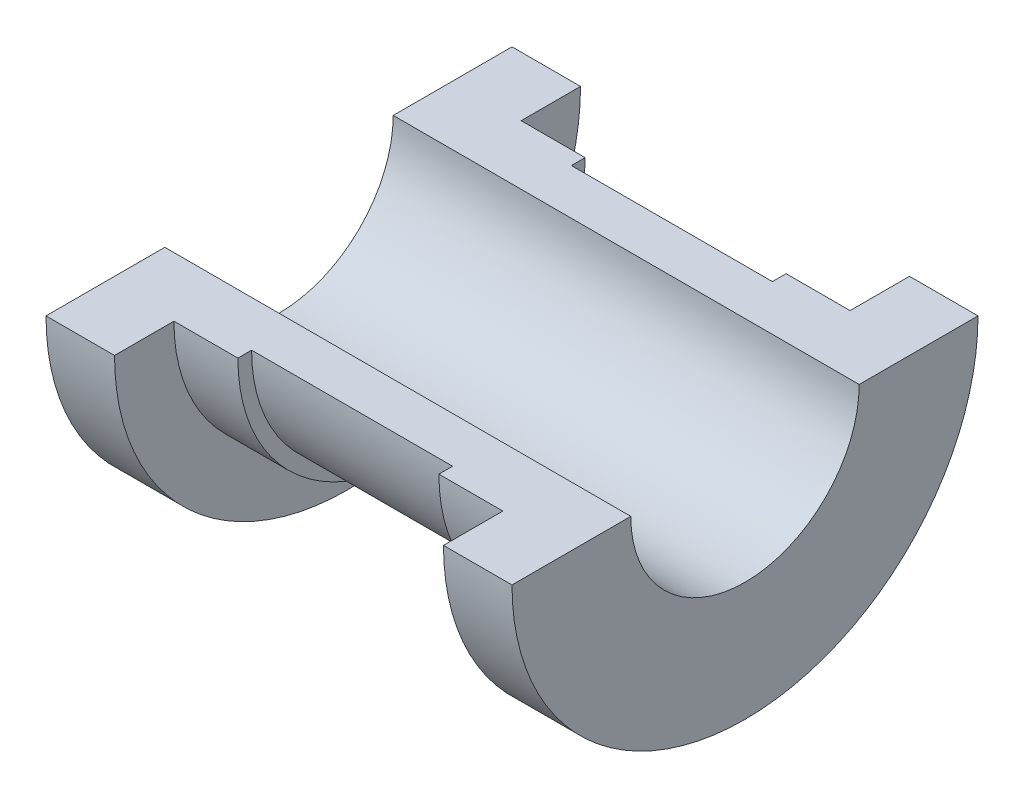
SolidWorks part; units mm, degrees
ref_plane "Front Plane" through (0, 0, 0) normal (0, 0, 1) x (1, 0, 0)
ref_plane "Top Plane" through (0, 0, 0) normal (0, 1, 0) x (1, 0, 0)
ref_plane "Right Plane" through (0, 0, 0) normal (1, 0, 0) x (0, 0, -1)
sketch "Sketch2" plane through (0, 0, 0) normal (0, 1, 0) x (1, 0, 0)
  line L0 (0, 0) -> (0, 66.6493) construction
  line L1 (25.5, 0) -> (-25.5, 0)
  line L2 (-25.5, 0) -> (-25.5, 25.5)
  line L3 (-18, 25.5) -> (-18, 19)
  line L4 (-18, 19) -> (-11, 19)
  line L5 (-11, 19) -> (-11, 17.5)
  line L6 (-11, 17.5) -> (11, 17.5)
  line L7 (-25.5, 25.5) -> (-18, 25.5)
  line L8 (25.5, 25.5) -> (18, 25.5)
  line L9 (11, 19) -> (11, 17.5)
  line L10 (18, 19) -> (11, 19)
  line L11 (18, 25.5) -> (18, 19)
  line L12 (25.5, 0) -> (25.5, 25.5)
  point P13 (0, 17.5)
  dimension "D1" = 51
  dimension "D2" = 22
  dimension "D3" = 36
  dimension "D4" = 25.5
  dimension "D5" = 19
  dimension "D6" = 17.5
revolve "Revolve3" add sketch "Sketch2" angle 180 about L1
sketch "Sketch3" plane through (-25.5, 0, 0) normal (-1, 0, 0) x (0, 0, 1)
  line L0 (25.5, 0) -> (-25.5, 0) construction
  line L1 (12.5, 0) -> (-12.5, 0)
  arc A0 (-12.5, 0) -> (12.5, 0) centre (0, 0) ccw
  dimension "D1" = 25
extrude "Cut-Extrude1" cut sketch "Sketch3" against normal through all contours A0 L1
ref_plane "Plane2" through (0, -17.5, 0) normal (0, -1, 0) x (-1, 0, 0)
sketch "Sketch11" plane through (0, -17.5, 0) normal (0, -1, 0) x (-1, 0, 0)
  circle A0 centre (0, 0) radius 3
  dimension "D1" = 6
extrude "Boss-Extrude2" add sketch "Sketch11" along normal blind 6 separate body
